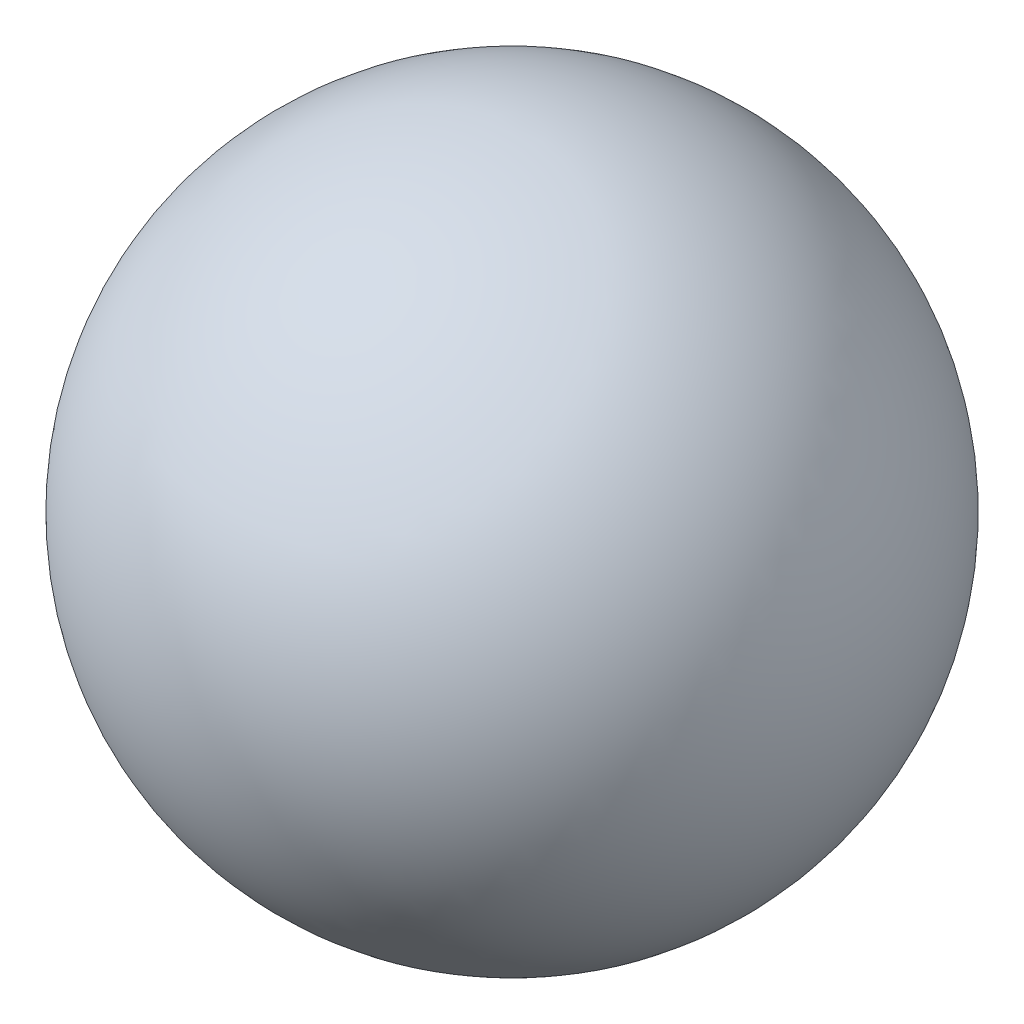
SolidWorks part; units mm, degrees
ref_plane "Front Plane" through (0, 0, 0) normal (0, 0, 1) x (1, 0, 0)
ref_plane "Top Plane" through (0, 0, 0) normal (0, 1, 0) x (1, 0, 0)
ref_plane "Right Plane" through (0, 0, 0) normal (1, 0, 0) x (0, 0, -1)
sketch "Sketch1" plane through (0, 0, 0) normal (0, 0, 1) x (1, 0, 0)
  line L0 (0, 0.24) -> (0, -0.24)
  line L1 (0, 0.951) -> (0, -0.951) construction
  arc A0 (0, 0.24) -> (0, -0.24) centre (0, 0) cw
  point P4 (0, 0)
  point P8 (0, 0)
  dimension "D1" = 0.48
revolve "Revolve1" add sketch "Sketch1" angle 360 about L1
